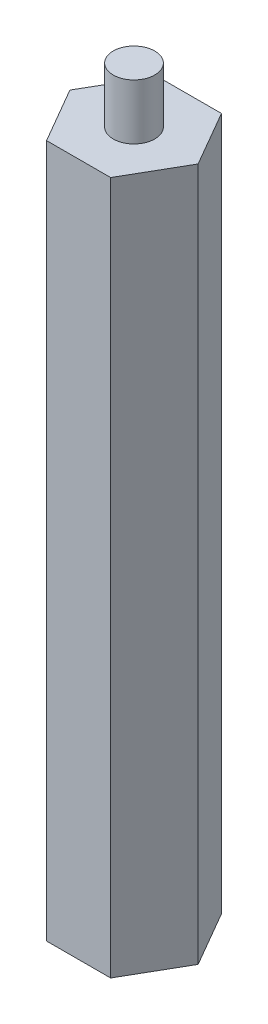
SolidWorks part; units mm, degrees
ref_plane "前视基准面" through (0, 0, 0) normal (0, 0, 1) x (1, 0, 0)
ref_plane "上视基准面" through (0, 0, 0) normal (0, 1, 0) x (1, 0, 0)
ref_plane "右视基准面" through (0, 0, 0) normal (1, 0, 0) x (0, 0, -1)
sketch "草图1" plane through (0, 0, 0) normal (0, 1, 0) x (1, 0, 0)
  line L1 (4.6107, 8.0047) -> (-4.6269, 7.9953)
  line L2 (-4.6269, 7.9953) -> (-9.2376, -0.0094)
  line L3 (-9.2376, -0.0094) -> (-4.6107, -8.0047)
  line L4 (-4.6107, -8.0047) -> (4.6269, -7.9953)
  line L5 (4.6269, -7.9953) -> (9.2376, 0.0094)
  line L6 (9.2376, 0.0094) -> (4.6107, 8.0047)
  circle A0 centre (0, 0) radius 8 construction
extrude "凸台-拉伸1" add sketch "草图1" along normal blind 100
sketch "草图2" plane through (0, 100, 0) normal (0, 1, 0) x (1, 0, 0)
  circle A0 centre (0, 0) radius 3
extrude "凸台-拉伸2" add sketch "草图2" along normal blind 8 contours A0
sketch "草图3" plane through (0, 0, 0) normal (0, -1, 0) x (1, 0, 0)
  circle A0 centre (0, 0) radius 3
extrude "切除-拉伸1" cut sketch "草图3" against normal blind 8
